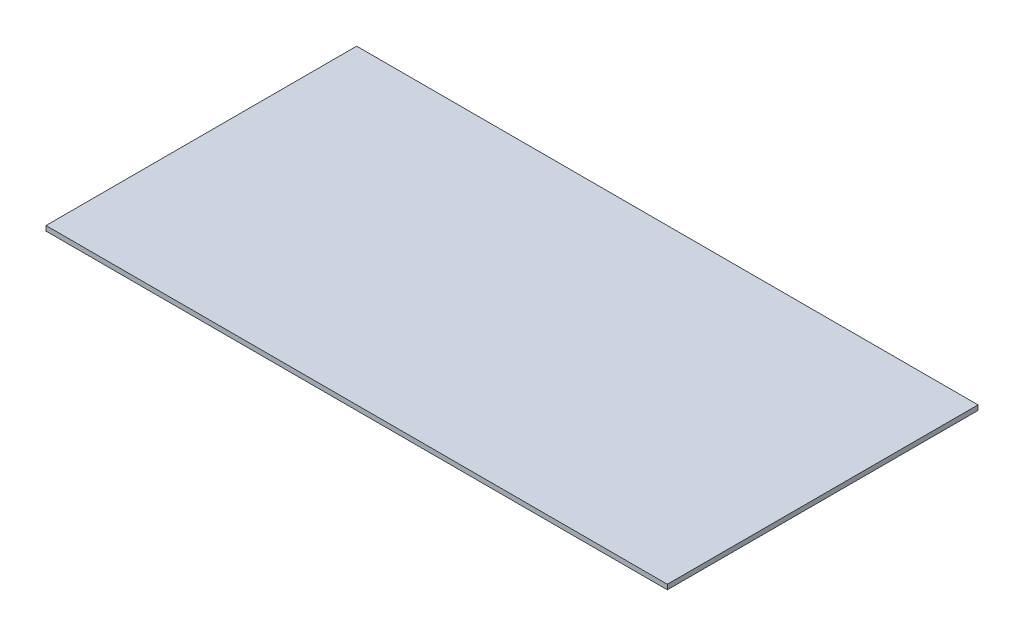
SolidWorks part; units mm, degrees
ref_plane "Front Plane" through (0, 0, 0) normal (0, 0, 1) x (1, 0, 0)
ref_plane "Top Plane" through (0, 0, 0) normal (0, 1, 0) x (1, 0, 0)
ref_plane "Right Plane" through (0, 0, 0) normal (1, 0, 0) x (0, 0, -1)
sketch "Sketch1" plane through (0, 0, 0) normal (0, 1, 0) x (1, 0, 0)
  line L1 (-1219.2, -609.6) -> (1219.2, -609.6)
  line L2 (-1219.2, -609.6) -> (-1219.2, 609.6)
  line L3 (-1219.2, 609.6) -> (1219.2, 609.6)
  line L4 (1219.2, -609.6) -> (1219.2, 609.6)
  line L5 (-1219.2, -609.6) -> (1219.2, 609.6) construction
  line L6 (-1219.2, 609.6) -> (1219.2, -609.6) construction
  point P0 (0, 0)
  dimension "D1" = 1219.2
  dimension "D2" = 2438.4
extrude "Boss-Extrude1" add sketch "Sketch1" along normal blind 19.05
